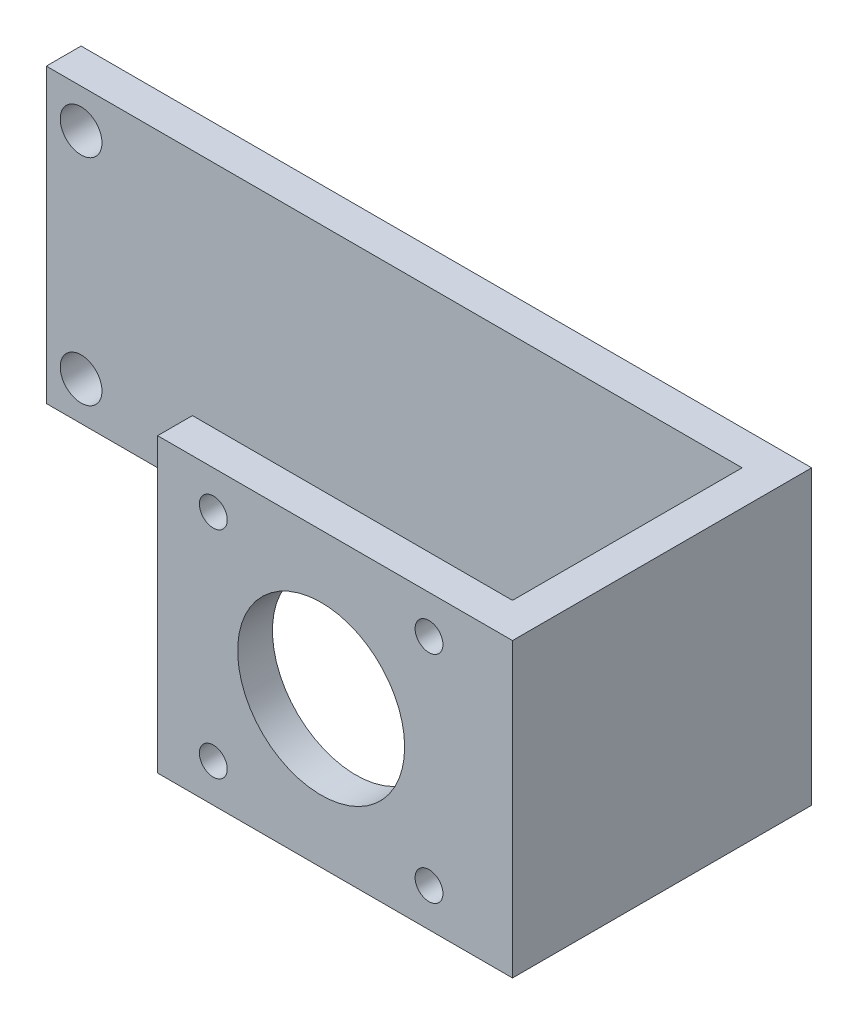
SolidWorks part; units mm, degrees
ref_plane "Alzado" through (0, 0, 0) normal (0, 0, 1) x (1, 0, 0)
ref_plane "Planta" through (0, 0, 0) normal (0, 1, 0) x (1, 0, 0)
ref_plane "Vista lateral" through (0, 0, 0) normal (1, 0, 0) x (0, 0, -1)
sketch "Croquis1" plane through (0, 0, 0) normal (0, 0, 1) x (1, 0, 0)
  line L0 (-47.5, -21) -> (-47.5, 21)
  line L1 (-52.5, 21) -> (52.5, 21)
  line L2 (-52.5, 21) -> (-52.5, -21)
  line L3 (-52.5, -21) -> (52.5, -21)
  line L4 (52.5, 21) -> (52.5, -21)
  line L5 (-52.5, 21) -> (52.5, -21) construction
  line L6 (-52.5, -21) -> (52.5, 21) construction
  line L7 (-52.5, 0) -> (52.5, 0) construction
  circle A0 centre (-47.5, 15.44) radius 3
  circle A1 centre (-47.5, -15.44) radius 3
  point P0 (0, 0)
  dimension "D1" = 42
  dimension "D2" = 105
  dimension "D3" = 5
extrude "Saliente-Extruir1" add sketch "Croquis1" along normal blind 5
sketch "Croquis4" plane through (0, 0, 5) normal (0, 0, 1) x (1, 0, 0)
  line L0 (20, -21) -> (20, 21) construction
  line L4 (-52.5, -21) -> (52.5, -21) construction
  line L5 (-52.5, 21) -> (52.5, 21) construction
  line L6 (-52.5, 21) -> (-52.5, -21) construction
  dimension "D1" = 72.5
sketch "Croquis5" plane through (0, 0, 5) normal (0, 0, 1) x (1, 0, 0)
  line L0 (-52.5, -21) -> (52.5, -21) construction
  line L1 (47.5, -21) -> (52.5, -21)
  line L2 (47.5, -21) -> (47.5, 21)
  line L3 (47.5, 21) -> (52.5, 21)
  line L4 (52.5, -21) -> (52.5, 21)
  dimension "D1" = 5
extrude "Saliente-Extruir2" add sketch "Croquis5" along normal blind 38
sketch "Croquis7" plane through (0, 0, 5) normal (0, 0, 1) x (1, 0, 0)
  line L0 (-52.5, 0) -> (25, 0) construction
  line L1 (-52.5, 21) -> (-52.5, -21) construction
  dimension "D1" = 77.5
sketch "Croquis8" plane through (47.5, 0, 0) normal (-1, 0, 0) x (0, 0, 1)
  line L0 (43, -21) -> (5, -21) construction
  line L1 (38, -21) -> (43, -21)
  line L2 (38, -21) -> (38, 21)
  line L3 (38, 21) -> (43, 21)
  line L4 (43, -21) -> (43, 21)
  dimension "D1" = 5
extrude "Saliente-Extruir3" add sketch "Croquis8" along normal blind 46
sketch "Croquis10" plane through (0, 0, 43) normal (0, 0, 1) x (1, 0, 0)
  line L1 (9.5, 15.5) -> (40.5, 15.5)
  line L2 (9.5, 15.5) -> (9.5, -15.5)
  line L3 (9.5, -15.5) -> (40.5, -15.5)
  line L4 (40.5, 15.5) -> (40.5, -15.5)
  line L5 (9.5, 15.5) -> (40.5, -15.5) construction
  line L6 (9.5, -15.5) -> (40.5, 15.5) construction
  circle A0 centre (9.5, 15.5) radius 2
  circle A1 centre (9.5, -15.5) radius 2
  circle A2 centre (40.5, -15.5) radius 2
  circle A3 centre (40.5, 15.5) radius 2
  circle A4 centre (25, 0) radius 12
  point P0 (25, 0)
  dimension "D3" = 4
  dimension "D4" = 24
  dimension "D1" = 31
  dimension "D2" = 31
extrude "Cortar-Extruir1" cut sketch "Croquis10" against normal up to surface (5 mm away) contours A0 | A1 | A4 | A2 | A3 up to face at (24.5, 0, 38)
